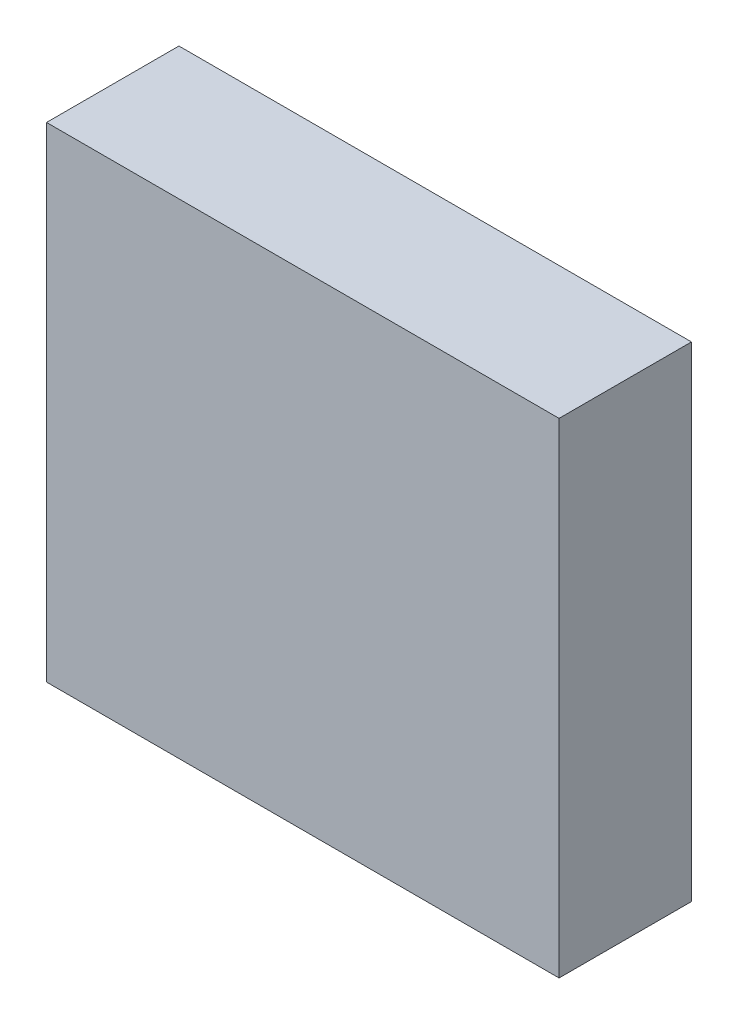
SolidWorks part; units mm, degrees
ref_plane "Přední rovina" through (0, 0, 0) normal (0, 0, 1) x (1, 0, 0)
ref_plane "Horní rovina" through (0, 0, 0) normal (0, 1, 0) x (1, 0, 0)
ref_plane "Pravá rovina" through (0, 0, 0) normal (1, 0, 0) x (0, 0, -1)
sketch "Skica1" plane through (0, 0, 0) normal (0, 0, 1) x (1, 0, 0)
  line L1 (-67.3279, 26.7208) -> (-28.6144, 26.7208)
  line L2 (-67.3279, 26.7208) -> (-67.3279, -9.8888)
  line L3 (-67.3279, -9.8888) -> (-28.6144, -9.8888)
  line L4 (-28.6144, 26.7208) -> (-28.6144, -9.8888)
extrude "Přidat vysunutím1" add sketch "Skica1" along normal blind 10
